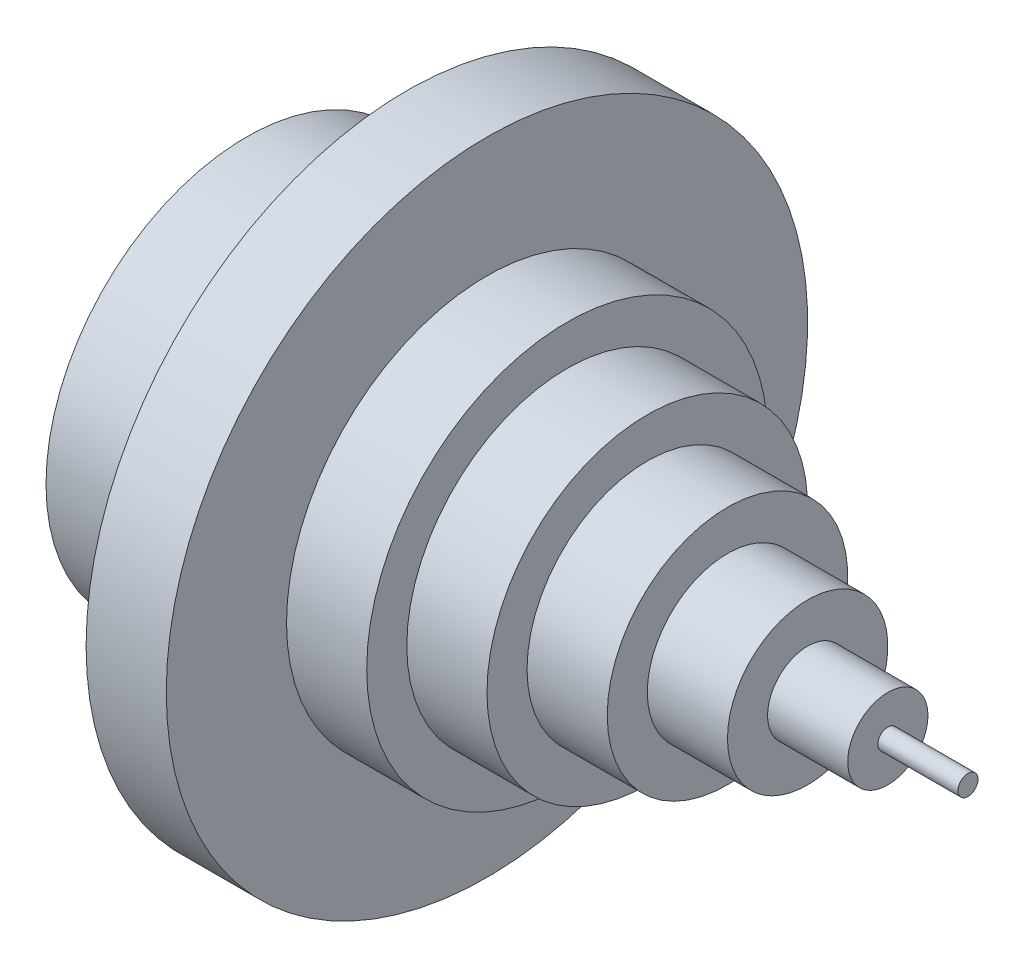
SolidWorks part; units mm, degrees
ref_plane "Front Plane" through (0, 0, 0) normal (0, 0, 1) x (1, 0, 0)
ref_plane "Top Plane" through (0, 0, 0) normal (0, 1, 0) x (1, 0, 0)
ref_plane "Right Plane" through (0, 0, 0) normal (1, 0, 0) x (0, 0, -1)
sketch "Sketch2" plane through (0, 0, 0) normal (0, 0, 1) x (1, 0, 0)
  line L0 (-106.9668, 0) -> (122.8138, 0) construction
  line L1 (40, 50) -> (40, 80)
  line L2 (40, 80) -> (60, 80)
  line L3 (60, 80) -> (60, 50)
  line L4 (60, 50) -> (80, 50)
  line L5 (80, 50) -> (80, 40)
  line L6 (80, 40) -> (100, 40)
  line L7 (100, 40) -> (100, 30)
  line L8 (100, 30) -> (120, 30)
  line L9 (120, 30) -> (120, 20)
  line L10 (120, 20) -> (140, 20)
  line L11 (140, 20) -> (140, 10)
  line L12 (140, 10) -> (160, 10)
  line L13 (160, 10) -> (160, 2.5)
  line L14 (160, 2.5) -> (180, 2.5)
  line L15 (180, 2.5) -> (180, 0)
  line L16 (40, 50) -> (0, 50)
  line L17 (0, 50) -> (0, 0)
  line L18 (0, 0) -> (180, 0)
  dimension "D1" = 20
  dimension "D2" = 5
  dimension "D3" = 10
  dimension "D4" = 20
  dimension "D5" = 30
  dimension "D6" = 50
  dimension "D7" = 80
  dimension "D8" = 50
  dimension "D9" = 40
  dimension "D10" = 20
  dimension "D11" = 20
  dimension "D12" = 20
  dimension "D13" = 20
  dimension "D14" = 20
  dimension "D15" = 20
  dimension "D16" = 40
revolve "Revolve4" add sketch "Sketch2" angle 360 about L0
sketch "Sketch8" plane through (0, 0, 0) normal (-1, 0, 0) x (0, 0, 1)
  circle A0 centre (0, 0) radius 40
  dimension "D1" = 80
extrude "Cut-Extrude3" cut sketch "Sketch8" against normal blind 40
